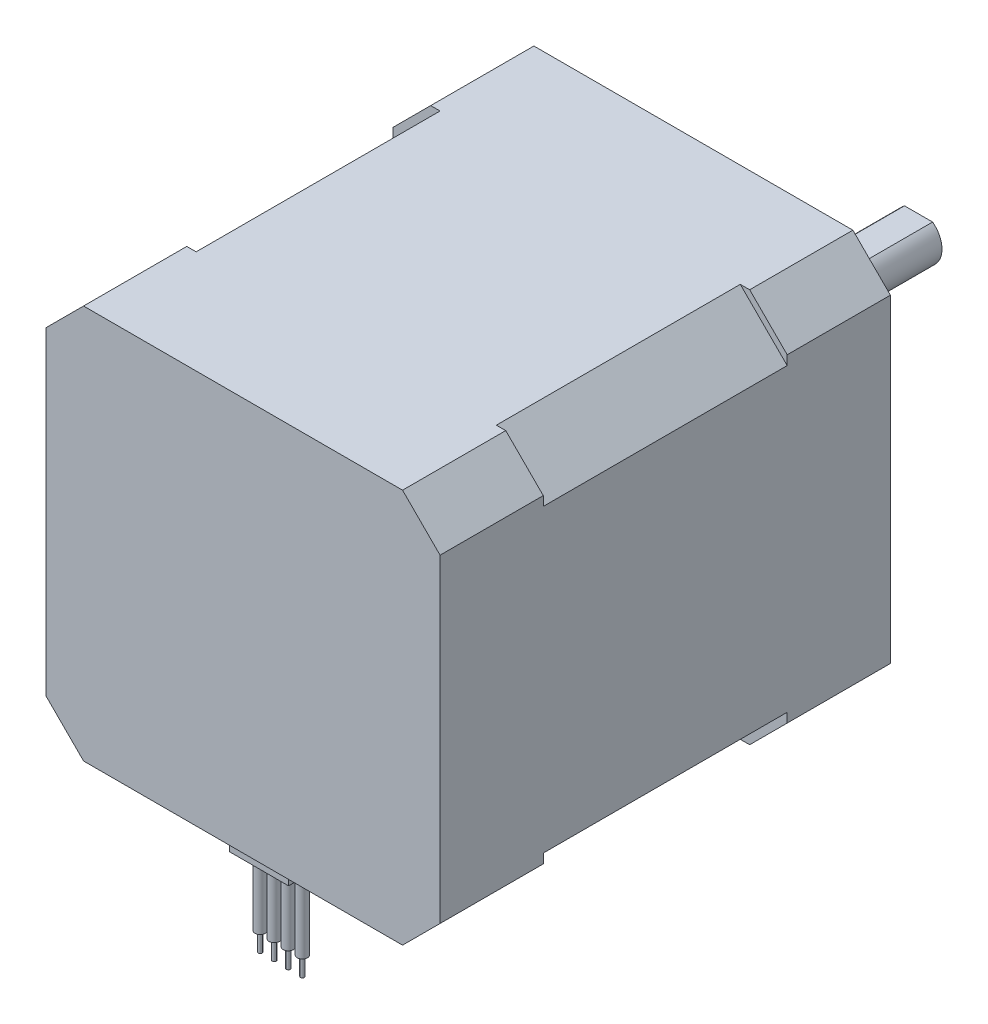
SolidWorks part; units mm, degrees
ref_plane "Plan de face" through (0, 0, 0) normal (0, 0, 1) x (1, 0, 0)
ref_plane "Plan de dessus" through (0, 0, 0) normal (0, 1, 0) x (1, 0, 0)
ref_plane "Plan de droite" through (0, 0, 0) normal (1, 0, 0) x (0, 0, -1)
sketch "Esquisse1" plane through (0, 0, 0) normal (0, 0, 1) x (1, 0, 0)
  line L0 (17, 21) -> (21, 17)
  line L1 (-17, 21) -> (17, 21)
  line L2 (-21, 17) -> (-21, -17)
  line L3 (-17, -21) -> (17, -21)
  line L4 (21, 17) -> (21, -17)
  line L5 (-21, 21) -> (21, -21) construction
  line L6 (-21, -21) -> (21, 21) construction
  line L7 (-21, 17) -> (-17, 21)
  line L8 (-21, -17) -> (-17, -21)
  line L9 (17, -21) -> (21, -17)
  point P0 (0, 0)
  dimension "D1" = 42
  dimension "D2" = 42
extrude "Boss.-Extru.1" add sketch "Esquisse1" along normal blind 11
sketch "Esquisse2" plane through (0, 0, 0) normal (0, 0, -1) x (-1, 0, 0)
  line L0 (-16, 21) -> (16, 21)
  line L1 (-17, 21) -> (17, 21) construction
  line L2 (16, 21) -> (21, 16)
  line L3 (21, 17) -> (21, -17) construction
  line L4 (21, 16) -> (21, -16)
  line L5 (21, -16) -> (16, -21)
  line L6 (17, -21) -> (-17, -21) construction
  line L7 (16, -21) -> (-16, -21)
  line L8 (-16, -21) -> (-21, -16)
  line L9 (-21, -17) -> (-21, 17) construction
  line L10 (-21, -16) -> (-21, 16)
  line L11 (-21, 16) -> (-16, 21)
  line L12 (0, 0) -> (0, 21) construction
  dimension "D1" = 5
extrude "Boss.-Extru.2" add sketch "Esquisse2" along normal blind 26
sketch "Esquisse3" plane through (0, 0, -26) normal (0, 0, -1) x (-1, 0, 0)
  line L0 (-17, 21) -> (-21, 17)
  line L1 (-21, 17) -> (-21, -17)
  line L2 (-21, -17) -> (-17, -21)
  line L3 (-17, -21) -> (17, -21)
  line L4 (17, -21) -> (21, -17)
  line L5 (21, -17) -> (21, 17)
  line L6 (21, 17) -> (17, 21)
  line L7 (17, 21) -> (-17, 21)
extrude "Boss.-Extru.3" add sketch "Esquisse3" along normal blind 11
sketch "Esquisse4" plane through (0, 0, -37) normal (0, 0, -1) x (-1, 0, 0)
  circle A0 centre (0, 0) radius 11
  dimension "D1" = 22
extrude "Boss.-Extru.4" add sketch "Esquisse4" along normal blind 2
sketch "Esquisse5" plane through (0, 0, -39) normal (0, 0, -1) x (-1, 0, 0)
  circle A0 centre (0, 0) radius 2.5
  dimension "D1" = 5
extrude "Boss.-Extru.5" add sketch "Esquisse5" along normal blind 22
sketch "Esquisse6" plane through (0, 0, -61) normal (0, 0, -1) x (-1, 0, 0)
  line L0 (0, 0) -> (0, 2) construction
  line L1 (-2.8992, 3) -> (2.8992, 3)
  line L2 (-2.8992, 3) -> (-2.8992, 2)
  line L3 (-2.8992, 2) -> (2.8992, 2)
  line L4 (2.8992, 3) -> (2.8992, 2)
  line L5 (-2.8992, 3) -> (2.8992, 2) construction
  line L6 (-2.8992, 2) -> (2.8992, 3) construction
  line L7 (0, 2) -> (0, 2.5) construction
  line L8 (0, 0) -> (0, -2.5) construction
  circle A0 centre (0, 0) radius 2.5 construction
  circle A1 centre (0, 0) radius 2.5 construction
  point P0 (0, 2.5)
  dimension "D1" = 4.5
extrude "Enlèv. mat.-Extru.1" cut sketch "Esquisse6" against normal blind 18
hole_wizard "Trou taraudé M31" positions "Esquisse7" profile "Esquisse8" tap size "M3" standard "ISO"
sketch "Esquisse7" plane through (0, 0, -37) normal (0, 0, -1) x (-1, 0, 0)
  line L0 (-15.5, 15.5) -> (15.5, 15.5) construction
  line L1 (15.5, 15.5) -> (15.5, -15.5) construction
  line L2 (15.5, -15.5) -> (-15.5, -15.5) construction
  line L3 (-15.5, -15.5) -> (-15.5, 15.5) construction
  line L4 (-15.5, 15.5) -> (15.5, -15.5) construction
  point P0 (-15.5, 15.5)
  point P2 (15.5, 15.5)
  point P4 (15.5, -15.5)
  point P6 (-15.5, -15.5)
  dimension "D1" = 31
  dimension "D2" = 31
sketch "Esquisse8" plane through (15.5, 15.5, -37) normal (1, 0, 0) x (0, 1, 0)
  line L0 (0, 0) -> (0, 7.7511)
  line L1 (0, 7.7511) -> (1.25, 7)
  line L2 (1.25, 7) -> (1.25, 0)
  line L5 (1.25, 0) -> (0, 0)
  line L10 (0, 7.7511) -> (-1.25, 7) construction
  line L11 (0, -6.35) -> (0, 107.95) construction
  dimension "Diamètre du trou pour taraudage" = 2.5
  dimension "Profondeur du trou pour taraudage" = 7
  dimension "Angle de pointe" = 118
cosmetic thread "Filetage de perçage1" parameters "D1"=4.5, "D2"=3
cosmetic thread "Filetage de perçage2" parameters "D1"=4.5, "D2"=3
cosmetic thread "Filetage de perçage3" parameters "D1"=4.5, "D2"=3
cosmetic thread "Filetage de perçage4" parameters "D1"=4.5, "D2"=3
sketch "Esquisse9" plane through (0, -21, 0) normal (0, -1, 0) x (1, 0, 0)
  line L0 (0, 0) -> (0, 4.55) construction
  line L1 (-3.15, 9.3) -> (3.15, 9.3)
  line L2 (-3.15, 9.3) -> (-3.15, 4.55)
  line L3 (-3.15, 4.55) -> (3.15, 4.55)
  line L4 (3.15, 9.3) -> (3.15, 4.55)
  line L5 (0, 4.55) -> (0, 9.3) construction
  line L6 (-17, 11) -> (17, 11) construction
  dimension "D1" = 6.3
  dimension "D2" = 4.75
  dimension "D3" = 1.7
extrude "Boss.-Extru.6" add sketch "Esquisse9" along normal blind 2.3
sketch "Esquisse10" plane through (0, -23.3, 0) normal (0, -1, 0) x (1, 0, 0)
  line L0 (-2.25, 6.925) -> (-0.75, 6.925) construction
  line L1 (-0.75, 6.925) -> (0.75, 6.925) construction
  line L2 (0.75, 6.925) -> (2.25, 6.925) construction
  line L3 (3.15, 6.925) -> (2.25, 6.925) construction
  line L4 (0, 6.925) -> (0, 0) construction
  line L5 (3.15, 4.55) -> (3.15, 9.3) construction
  circle A0 centre (-2.25, 6.925) radius 0.2025
  circle A1 centre (-0.75, 6.925) radius 0.2025
  circle A2 centre (0.75, 6.925) radius 0.2025
  circle A3 centre (2.25, 6.925) radius 0.2025
  dimension "D1" = 0.405
  dimension "D2" = 1.5
extrude "Boss.-Extru.7" add sketch "Esquisse10" along normal blind 10
sketch "Esquisse11" plane through (0, -23.3, 0) normal (0, -1, 0) x (1, 0, 0)
  circle A0 centre (-2.25, 6.925) radius 0.55
  circle A1 centre (-0.75, 6.925) radius 0.55
  circle A2 centre (0.75, 6.925) radius 0.55
  circle A3 centre (2.25, 6.925) radius 0.55
  dimension "D1" = 1.1
extrude "Boss.-Extru.8" add sketch "Esquisse11" along normal blind 8
